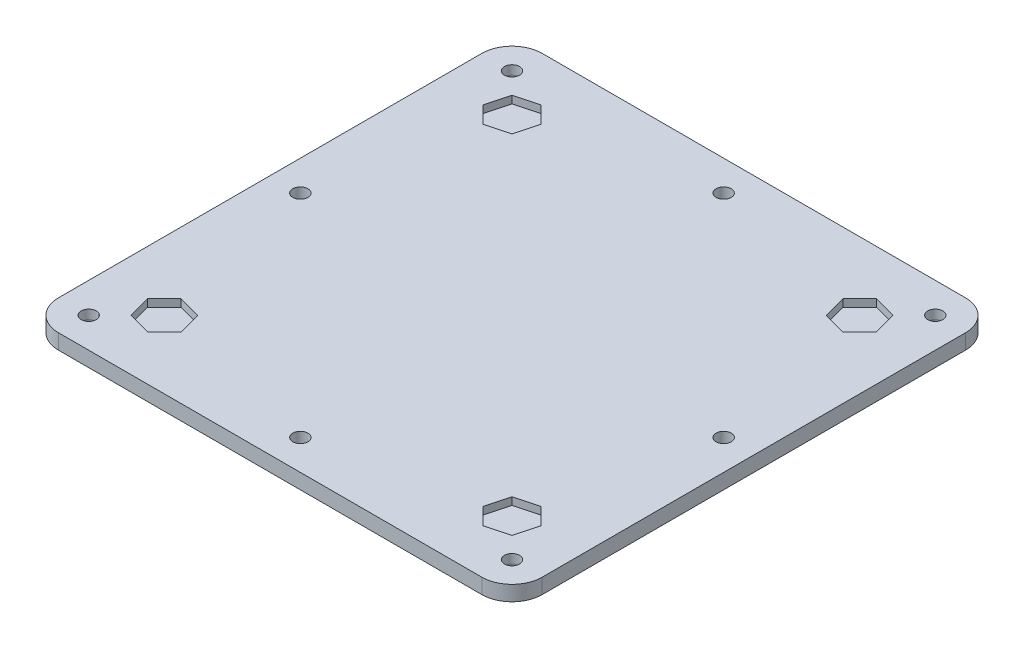
SolidWorks part; units mm, degrees
ref_plane "Front Plane" through (0, 0, 0) normal (0, 0, 1) x (1, 0, 0)
ref_plane "Top Plane" through (0, 0, 0) normal (0, 1, 0) x (1, 0, 0)
ref_plane "Right Plane" through (0, 0, 0) normal (1, 0, 0) x (0, 0, -1)
sketch "Sketch1" plane through (0, 0, 0) normal (0, 1, 0) x (1, 0, 0)
  line L1 (0, 0) -> (203.2, 0)
  line L2 (0, 0) -> (0, 203.2)
  line L3 (0, 203.2) -> (203.2, 203.2)
  line L4 (203.2, 0) -> (203.2, 203.2)
  dimension "D1" = 203.2
  dimension "D2" = 203.2
extrude "Boss-Extrude1" add sketch "Sketch1" along normal blind 6.35
fillet "Fillet1" radius 12.7 4 edges at (0, 3.175, -203.2) (0, 3.175, 0) (203.2, 3.175, 0) (203.2, 3.175, -203.2)
sketch "Sketch2" plane through (0, 0, 0) normal (0, -1, 0) x (1, 0, 0)
  circle A0 centre (12.7, -12.7) radius 3.175
  circle A1 centre (190.5, -12.7) radius 3.175
  circle A2 centre (190.5, -190.5) radius 3.175
  circle A3 centre (12.7, -190.5) radius 3.175
  arc A4 (190.5, -203.2) -> (203.2, -190.5) centre (190.5, -190.5) ccw construction
  arc A5 (12.7, 0) -> (0, -12.7) centre (12.7, -12.7) ccw construction
  dimension "D1" = 6.35
extrude "Cut-Extrude1" cut sketch "Sketch2" against normal through all
sketch "Sketch22" plane through (0, 6.35, 0) normal (0, 1, 0) x (1, 0, 0)
  line L17 (190.5, 203.2) -> (12.7, 203.2) construction
  line L18 (203.2, 12.7) -> (203.2, 190.5) construction
  line L21 (181.6542, 181.6542) -> (172.0521, 184.2271)
  line L22 (172.0521, 184.2271) -> (165.0229, 177.1979)
  line L23 (165.0229, 177.1979) -> (167.5958, 167.5958)
  line L24 (167.5958, 167.5958) -> (177.1979, 165.0229)
  line L25 (177.1979, 165.0229) -> (184.2271, 172.0521)
  line L26 (184.2271, 172.0521) -> (181.6542, 181.6542)
  line L27 (174.625, 174.625) -> (190.5, 190.5) construction
  line L28 (101.6, 203.2) -> (101.6, 0) construction
  line L29 (12.7, 0) -> (190.5, 0) construction
  line L30 (203.2, 101.6) -> (0, 101.6) construction
  line L31 (0, 190.5) -> (0, 12.7) construction
  line L32 (28.575, 174.625) -> (12.7, 190.5) construction
  line L33 (18.9729, 172.0521) -> (21.5458, 181.6542)
  line L34 (26.0021, 165.0229) -> (18.9729, 172.0521)
  line L35 (35.6042, 167.5958) -> (26.0021, 165.0229)
  line L36 (38.1771, 177.1979) -> (35.6042, 167.5958)
  line L37 (31.1479, 184.2271) -> (38.1771, 177.1979)
  line L38 (21.5458, 181.6542) -> (31.1479, 184.2271)
  line L39 (174.625, 28.575) -> (190.5, 12.7) construction
  line L40 (184.2271, 31.1479) -> (181.6542, 21.5458)
  line L41 (177.1979, 38.1771) -> (184.2271, 31.1479)
  line L42 (167.5958, 35.6042) -> (177.1979, 38.1771)
  line L43 (165.0229, 26.0021) -> (167.5958, 35.6042)
  line L44 (172.0521, 18.9729) -> (165.0229, 26.0021)
  line L45 (181.6542, 21.5458) -> (172.0521, 18.9729)
  line L46 (28.575, 28.575) -> (12.7, 12.7) construction
  line L47 (21.5458, 21.5458) -> (31.1479, 18.9729)
  line L48 (31.1479, 18.9729) -> (38.1771, 26.0021)
  line L49 (38.1771, 26.0021) -> (35.6042, 35.6042)
  line L50 (35.6042, 35.6042) -> (26.0021, 38.1771)
  line L51 (26.0021, 38.1771) -> (18.9729, 31.1479)
  line L52 (18.9729, 31.1479) -> (21.5458, 21.5458)
  circle A0 centre (174.625, 174.625) radius 8.609 construction
  circle A1 centre (28.575, 174.625) radius 8.609 construction
  circle A2 centre (174.625, 28.575) radius 8.609 construction
  circle A3 centre (28.575, 28.575) radius 8.609 construction
  dimension "D5" = 17.218
  dimension "D3" = 28.575
  dimension "D4" = 28.575
extrude "Cut-Extrude2" cut sketch "Sketch22" against normal blind 3.175
fillet "Fillet2" radius 2.54 4 edges at (12.7, 0, -15.875) (12.7, 0, -193.675) (190.5, 0, -193.675) (190.5, 0, -15.875)
sketch "Sketch23" plane through (0, 6.35, 0) normal (0, 1, 0) x (1, 0, 0)
  line L0 (21.5458, 21.5458) -> (181.6542, 181.6542) construction
  line L1 (21.5458, 181.6542) -> (181.6542, 21.5458) construction
  line L2 (203.2, 12.7) -> (203.2, 190.5) construction
  circle A0 centre (190.5, 101.6) radius 3.175
  circle A1 centre (101.6, 12.7) radius 3.175
  circle A2 centre (12.7, 101.6) radius 3.175
  circle A3 centre (101.6, 190.5) radius 3.175
  point P12 (203.2, 101.6)
  point P13 (101.6, 101.6)
  dimension "D3" = 6.35
  dimension "D2" = 12.7
  dimension "D1" = 4
extrude "Cut-Extrude3" cut sketch "Sketch23" against normal through all
